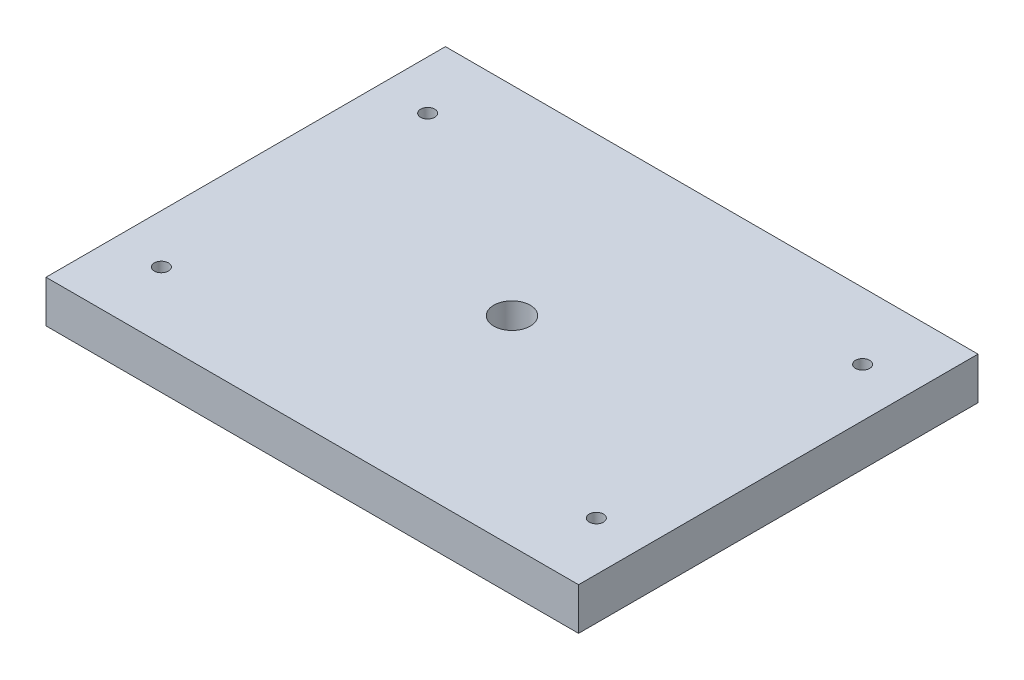
SolidWorks part; units mm, degrees
ref_plane "Front Plane" through (0, 0, 0) normal (0, 0, 1) x (1, 0, 0)
ref_plane "Top Plane" through (0, 0, 0) normal (0, 1, 0) x (1, 0, 0)
ref_plane "Right Plane" through (0, 0, 0) normal (1, 0, 0) x (0, 0, -1)
sketch "Sketch1" plane through (0, 0, 0) normal (0, 1, 0) x (1, 0, 0)
  line L1 (-60, -45) -> (60, -45)
  line L2 (-60, -45) -> (-60, 45)
  line L3 (-60, 45) -> (60, 45)
  line L4 (60, -45) -> (60, 45)
  line L5 (-60, -45) -> (60, 45) construction
  line L6 (-60, 45) -> (60, -45) construction
  point P0 (0, 0)
  dimension "D1" = 120
  dimension "D2" = 90
extrude "Boss-Extrude1" add sketch "Sketch1" along normal blind 9.5
sketch "Sketch2" plane through (0, 9.5, 0) normal (0, 1, 0) x (1, 0, 0)
  line L0 (-60, 0) -> (60, 0) construction
  line L1 (-60, 45) -> (-60, -45) construction
  line L2 (60, -45) -> (60, 45) construction
  line L3 (-60, -30) -> (60, -30) construction
  line L4 (-60, -45) -> (60, -45) construction
  line L5 (0, -45) -> (0, -18.8764) construction
  line L6 (-60, 30) -> (60, 30) construction
  circle A0 centre (-49, -30) radius 1.6
  circle A1 centre (49, -30) radius 1.6
  circle A2 centre (49, 30) radius 1.6
  circle A3 centre (-49, 30) radius 1.6
  dimension "D2" = 3.2
  dimension "D1" = 15
  dimension "D3" = 11
extrude "Cut-Extrude1" cut sketch "Sketch2" against normal through all
sketch "Sketch3" plane through (0, 9.5, 0) normal (0, 1, 0) x (1, 0, 0)
  circle A0 centre (0, 0) radius 4.1
  dimension "D1" = 8.2
extrude "Cut-Extrude2" cut sketch "Sketch3" against normal through all
